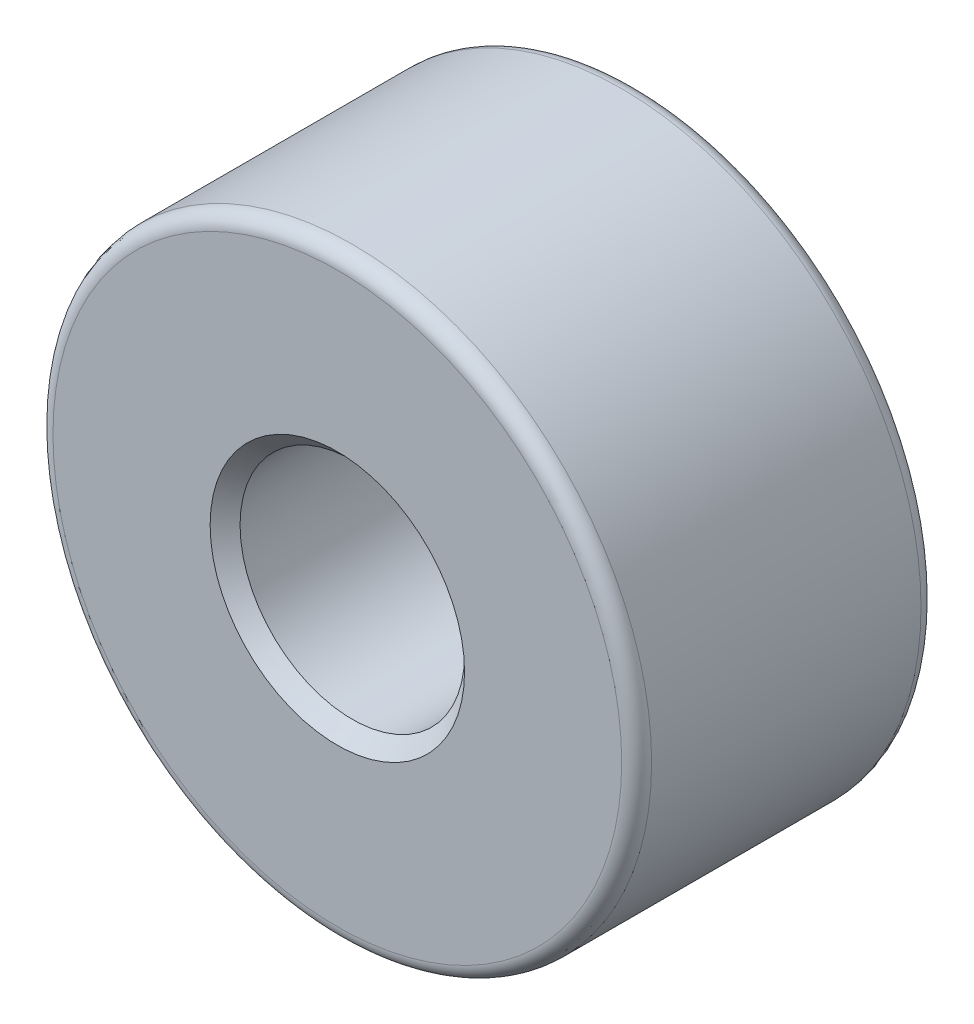
SolidWorks part; units mm, degrees
ref_plane "Ebene vorne" through (0, 0, 0) normal (0, 0, 1) x (1, 0, 0)
ref_plane "Ebene oben" through (0, 0, 0) normal (0, 1, 0) x (1, 0, 0)
ref_plane "Ebene rechts" through (0, 0, 0) normal (1, 0, 0) x (0, 0, -1)
sketch "Skizze1" plane through (0, 0, 0) normal (0, 0, 1) x (1, 0, 0)
  circle A0 centre (0, 0) radius 4
  circle A1 centre (0, 0) radius 1.5
  dimension "D1" = 3
  dimension "D2" = 8
extrude "Aufsatz-Linear austragen1" add sketch "Skizze1" along normal blind 4
chamfer "Fase1" distance 0.2 angle 45 2 edges at (1.5, 0, 0) (1.5, 0, 4)
fillet "Verrundung1" radius 0.2 2 edges at (4, 0, 0) (4, 0, 4)
